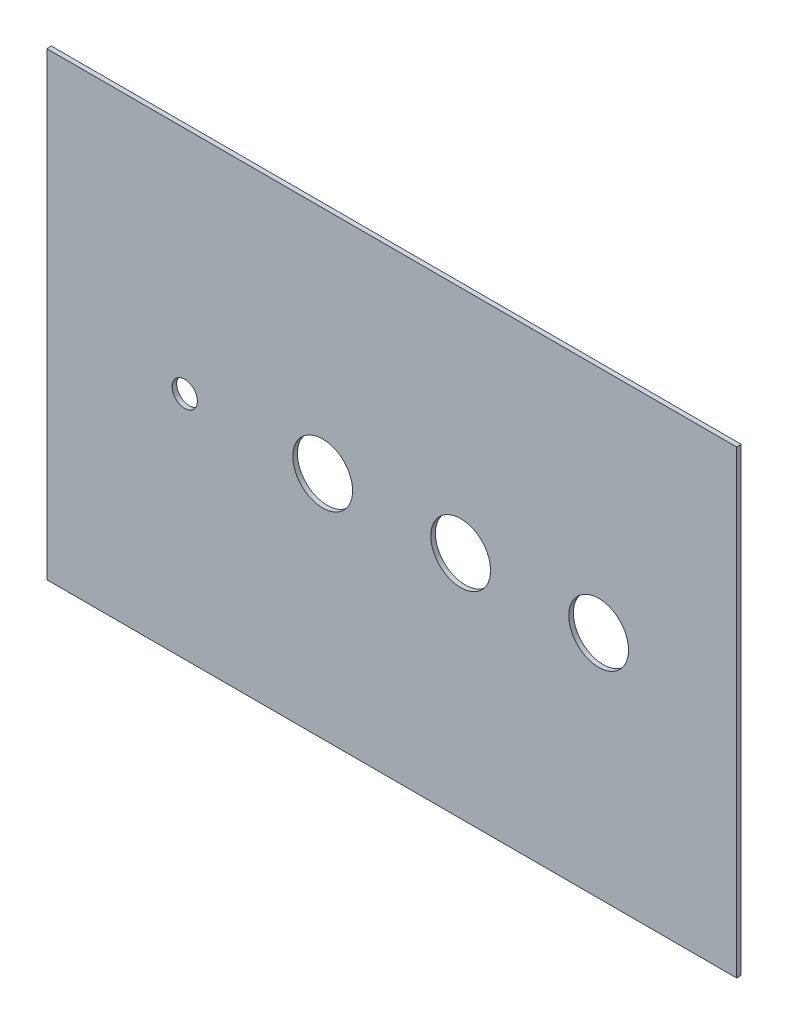
SolidWorks part; units mm, degrees
material "Plain Carbon Steel"
ref_plane "Front Plane" through (0, 0, 0) normal (0, 0, 1) x (1, 0, 0)
ref_plane "Top Plane" through (0, 0, 0) normal (0, 1, 0) x (1, 0, 0)
ref_plane "Right Plane" through (0, 0, 0) normal (1, 0, 0) x (0, 0, -1)
sketch "Sketch1" plane through (0, 0, 0) normal (0, 0, 1) x (1, 0, 0)
  line L1 (150, 100) -> (-150, 100)
  line L2 (150, 100) -> (150, -100)
  line L3 (150, -100) -> (-150, -100)
  line L4 (-150, 100) -> (-150, -100)
  line L10 (90, 0) -> (30, 0) construction
  line L12 (-30, 0) -> (-90, 0) construction
  circle A0 centre (30, 0) radius 13
  circle A1 centre (90, 0) radius 13
  circle A2 centre (-30, 0) radius 13
  circle A3 centre (-90, 0) radius 5.5
  point P0 (0, 0)
  dimension "D3" = 26
  dimension "D4" = 11
  dimension "D1" = 300
  dimension "D2" = 200
extrude "Boss-Extrude1" add sketch "Sketch1" along normal blind 2
